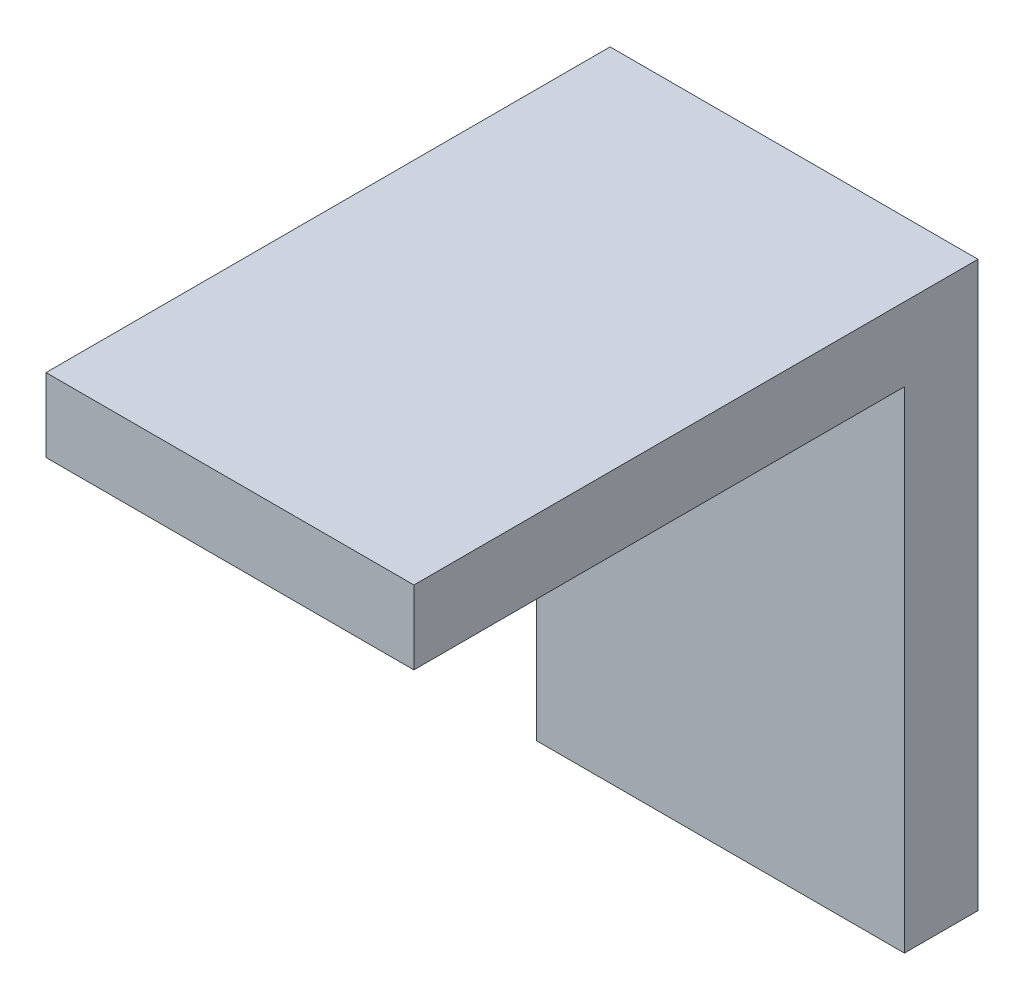
SolidWorks part; units mm, degrees
ref_plane "Front Plane" through (0, 0, 0) normal (0, 0, 1) x (1, 0, 0)
ref_plane "Top Plane" through (0, 0, 0) normal (0, 1, 0) x (1, 0, 0)
ref_plane "Right Plane" through (0, 0, 0) normal (1, 0, 0) x (0, 0, -1)
sketch "Sketch1" plane through (0, 0, 0) normal (1, 0, 0) x (0, 0, -1)
  line L0 (0, 0) -> (0, -40)
  line L1 (0, 0) -> (-40, 0)
  dimension "D1" = 40
  dimension "D2" = 40
extrude "Extrude-Thin1" add sketch "Sketch1" along normal blind 30 thin thin type one direction wall 6
